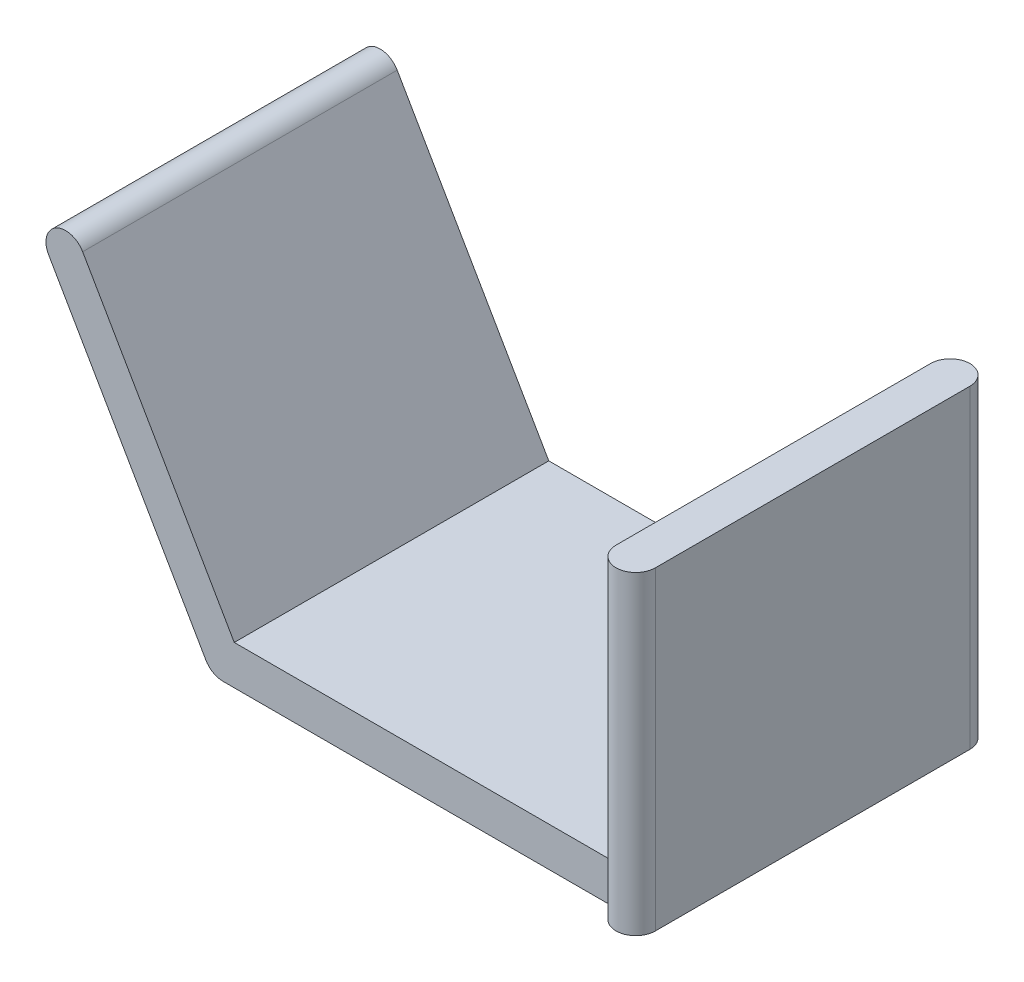
SolidWorks part; units mm, degrees
ref_plane "Front" through (0, 0, 0) normal (0, 0, 1) x (1, 0, 0)
ref_plane "Top" through (0, 0, 0) normal (0, 1, 0) x (1, 0, 0)
ref_plane "Right" through (0, 0, 0) normal (1, 0, 0) x (0, 0, -1)
sketch "草图10" plane through (0, 0, 0) normal (0, 0, 1) x (1, 0, 0)
  line L0 (-9, 0) -> (9, 0) construction
  line L1 (-8.4226, 1) -> (9, 1)
  line L2 (-9, -1) -> (9, -1)
  line L3 (-9, 0) -> (-14.848, 10.129) construction
  line L4 (-9, 0) -> (-17, 13.8564) construction
  line L5 (-9.866, -0.5) -> (-17.866, 13.3564)
  line L6 (-8.4226, 1) -> (-16.134, 14.3564)
  line L8 (9, 1) -> (16.5876, 1)
  line L10 (9, -1) -> (16.5876, -1)
  line L11 (16.5876, 1) -> (16.5876, -1)
  arc A0 (-9.866, -0.5) -> (-9, -1) centre (-9, 0) ccw
  arc A3 (-16.134, 14.3564) -> (-17.866, 13.3564) centre (-17, 13.8564) ccw
  point P2 (0, 0)
  point P10 (-13, 6.9282)
  dimension "D1" = 120
extrude "凸台-拉伸9" add sketch "草图10" along normal blind 16
sketch "草图12" plane through (0, 0, 16) normal (0, 0, 1) x (1, 0, 0)
  line L1 (16.5876, 1) -> (13, 1)
  line L2 (16.5876, 1) -> (16.5876, -1.4007)
  line L3 (16.5876, -1.4007) -> (13, -1.4007)
  line L4 (13, 1) -> (13, -1.4007)
extrude "切除-拉伸2" cut sketch "草图12" against normal blind 16
sketch "草图17" plane through (0, -1, 0) normal (0, -1, 0) x (1, 0, 0)
  line L0 (12, 17.4263) -> (12, -7.2194) construction
  line L1 (13, 0) -> (13, 16) construction
  line L2 (13, 8) -> (-0.2286, 8) construction
  line L4 (11, 16) -> (13, 16)
  line L5 (11, 16) -> (11, 0)
  line L6 (11, 0) -> (13, 0)
  line L7 (13, 16) -> (13, 0)
  dimension "D1" = 1
  dimension "D2" = 2
  dimension "D3" = 1
  dimension "D4" = 16
  dimension "D5" = 8
extrude "凸台-拉伸15" add sketch "草图17" against normal blind 16
sketch "草图18" plane through (0, 15, 0) normal (0, 1, 0) x (1, 0, 0)
  line L0 (11, 0) -> (13, 0) construction
  line L1 (13, -16) -> (11, -16) construction
  circle A0 centre (12, 0) radius 1
  circle A1 centre (12, -16) radius 1
extrude "凸台-拉伸16" add sketch "草图18" against normal blind 16
